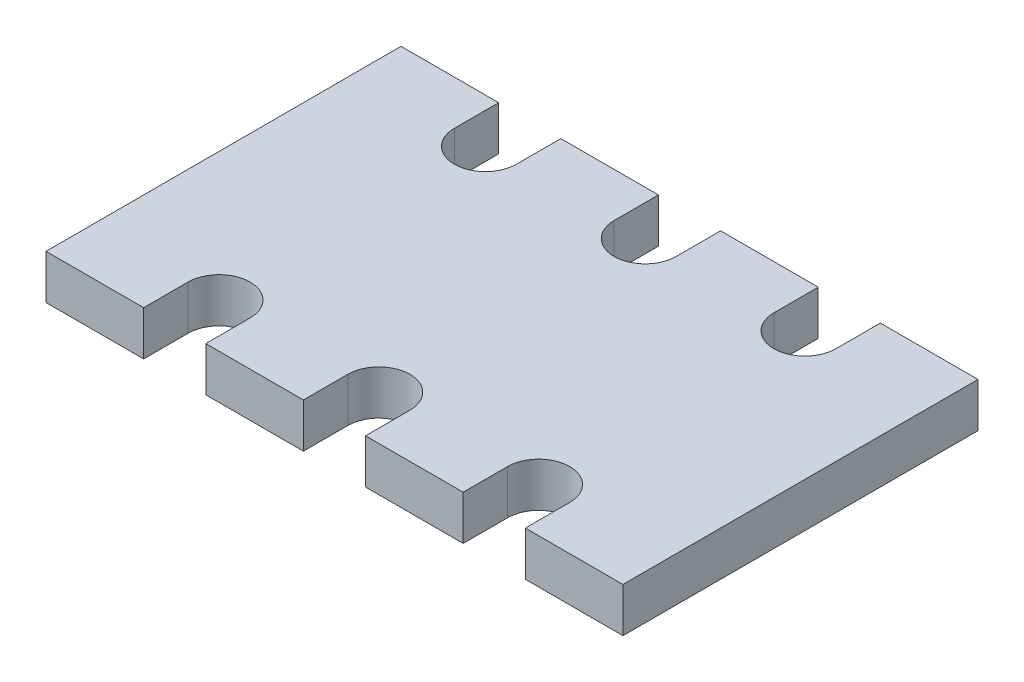
SolidWorks part; units mm, degrees
material "Polyether Polyol"
ref_plane "Front Plane" through (0, 0, 0) normal (0, 0, 1) x (1, 0, 0)
ref_plane "Top Plane" through (0, 0, 0) normal (0, 1, 0) x (1, 0, 0)
ref_plane "Right Plane" through (0, 0, 0) normal (1, 0, 0) x (0, 0, -1)
sketch "Sketch1" plane through (0, 0, 0) normal (0, 1, 0) x (1, 0, 0)
  line L0 (-5.4, 0) -> (-5.4, -0.5)
  line L1 (0, 0) -> (-1.1, 0)
  line L2 (0, 0) -> (0, -4)
  line L3 (0, -4) -> (-1.1, -4)
  line L4 (-6.5, 0) -> (-6.5, -4)
  line L5 (-1.8, -4) -> (-1.8, -3.5)
  line L6 (-4.7, -0.5) -> (-4.7, 0)
  line L7 (-1.8, 0) -> (-1.8, -0.5)
  line L8 (-5.4, -4) -> (-5.4, -3.5)
  line L9 (-1.1, -0.5) -> (-1.1, 0)
  line L11 (-5.4, 0) -> (-6.5, 0)
  line L12 (-3.6, -4) -> (-3.6, -3.5)
  line L13 (-2.9, -0.5) -> (-2.9, 0)
  line L14 (-3.6, -0.5) -> (-3.6, 0)
  line L15 (-5.4, -4) -> (-6.5, -4)
  line L18 (-1.1, -3.5) -> (-1.1, -4)
  line L22 (-4.7, -3.5) -> (-4.7, -4)
  line L24 (-2.9, 0) -> (-1.8, 0)
  line L25 (-3.6, 0) -> (-4.7, 0)
  line L27 (-2.9, -3.5) -> (-2.9, -4)
  line L28 (-2.9, -4) -> (-1.8, -4)
  line L29 (-3.6, -4) -> (-4.7, -4)
  arc A0 (-2.9, -3.5) -> (-3.6, -3.5) centre (-3.25, -3.5) ccw
  arc A1 (-5.4, -3.5) -> (-4.7, -3.5) centre (-5.05, -3.5) cw
  arc A2 (-1.1, -3.5) -> (-1.8, -3.5) centre (-1.45, -3.5) ccw
  arc A3 (-5.4, -0.5) -> (-4.7, -0.5) centre (-5.05, -0.5) ccw
  arc A4 (-2.9, -0.5) -> (-3.6, -0.5) centre (-3.25, -0.5) cw
  arc A5 (-1.8, -0.5) -> (-1.1, -0.5) centre (-1.45, -0.5) ccw
  dimension "D28" = 0.7
  dimension "D1" = 6.5
  dimension "D2" = 4
  dimension "D3" = 0.5
  dimension "D4" = 1.1
  dimension "D5" = 0.5
  dimension "D6" = 1.1
  dimension "D7" = 0.5
  dimension "D8" = 0.7
  dimension "D9" = 1.1
  dimension "D10" = 0.7
  dimension "D11" = 1.1
  dimension "D12" = 0.7
  dimension "D13" = 1.1
  dimension "D14" = 1.1
  dimension "D15" = 0.5
  dimension "D16" = 0.7
  dimension "D17" = 1.1
  dimension "D18" = 1.1
  dimension "D19" = 0.7
  dimension "D20" = 0.5
  dimension "D21" = 0.5
  dimension "D22" = 0
  dimension "D23" = 0.5
  dimension "D24" = 0.35
  dimension "D25" = 0.35
  dimension "D26" = 0.5
  dimension "D27" = 0.5
extrude "Boss-Extrude1" add sketch "Sketch1" along normal blind 0.5
